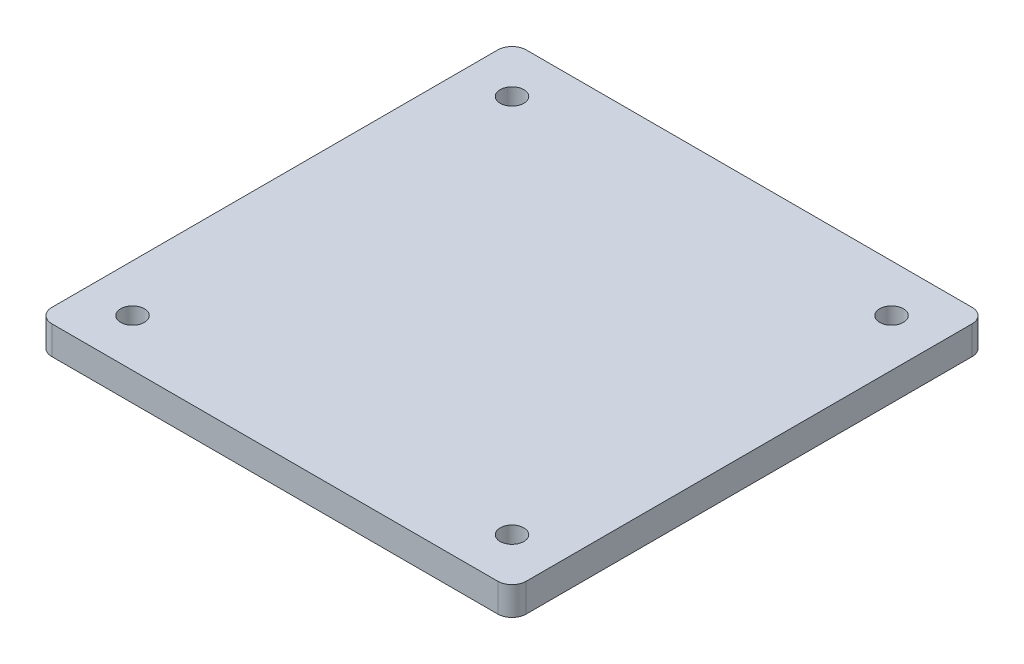
SolidWorks part; units mm, degrees
ref_plane "Front Plane" through (0, 0, 0) normal (0, 0, 1) x (1, 0, 0)
ref_plane "Top Plane" through (0, 0, 0) normal (0, 1, 0) x (1, 0, 0)
ref_plane "Right Plane" through (0, 0, 0) normal (1, 0, 0) x (0, 0, -1)
sketch "Sketch1" plane through (0, 0, 0) normal (0, 1, 0) x (1, 0, 0)
  line L1 (-10, 10) -> (90, 10)
  line L2 (-10, 10) -> (-10, -90)
  line L3 (-10, -90) -> (90, -90)
  line L4 (90, 10) -> (90, -90)
  circle A0 centre (0, 0) radius 2.5
  circle A1 centre (80, 0) radius 2.5
  circle A2 centre (80, -80) radius 2.5
  circle A3 centre (0, -80) radius 2.5
  dimension "D1" = 5
  dimension "D4" = 10
  dimension "D5" = 100
  dimension "D6" = 10
  dimension "D7" = 10
  dimension "D8" = 10
  dimension "D9" = 10
  dimension "D10" = 100
  dimension "D2" = 2
  dimension "D3" = 2
extrude "Boss-Extrude1" add sketch "Sketch1" along normal blind 6
fillet "Fillet1" radius 3 4 edges at (-10, 3, -10) (-10, 3, 90) (90, 3, -10) (90, 3, 90)
